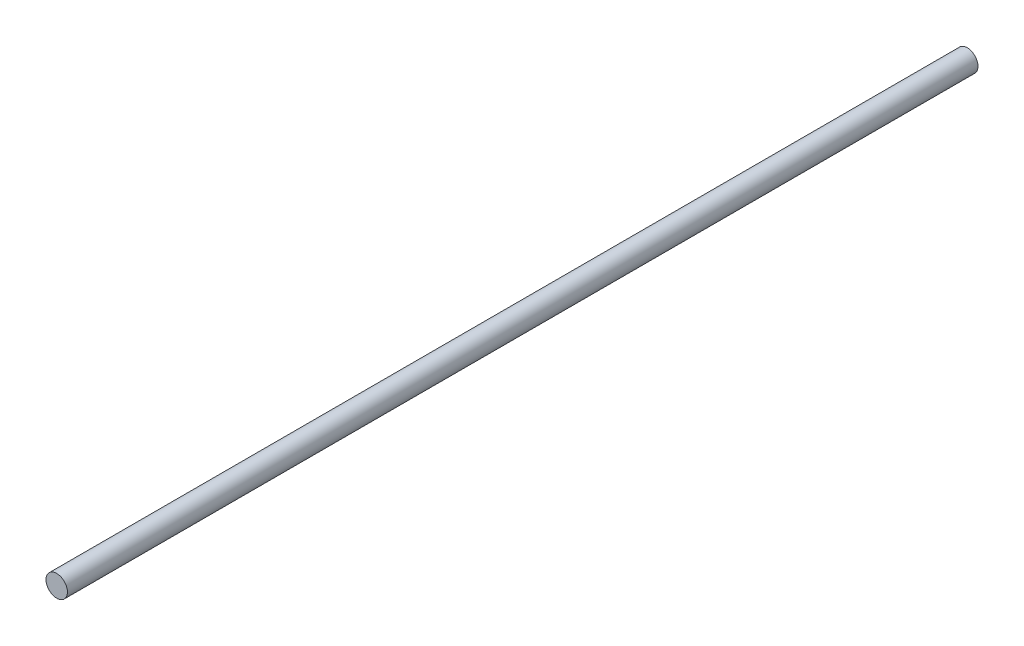
SolidWorks part; units mm, degrees
material "Plain Carbon Steel"
ref_plane "Front Plane" through (0, 0, 0) normal (0, 0, 1) x (1, 0, 0)
ref_plane "Top Plane" through (0, 0, 0) normal (0, 1, 0) x (1, 0, 0)
ref_plane "Right Plane" through (0, 0, 0) normal (1, 0, 0) x (0, 0, -1)
sketch "Sketch1" plane through (0, 0, 0) normal (0, 0, 1) x (1, 0, 0)
  circle A0 centre (0, 0) radius 6
  dimension "D1" = 12
extrude "Boss-Extrude1" add sketch "Sketch1" along normal blind 509.05
